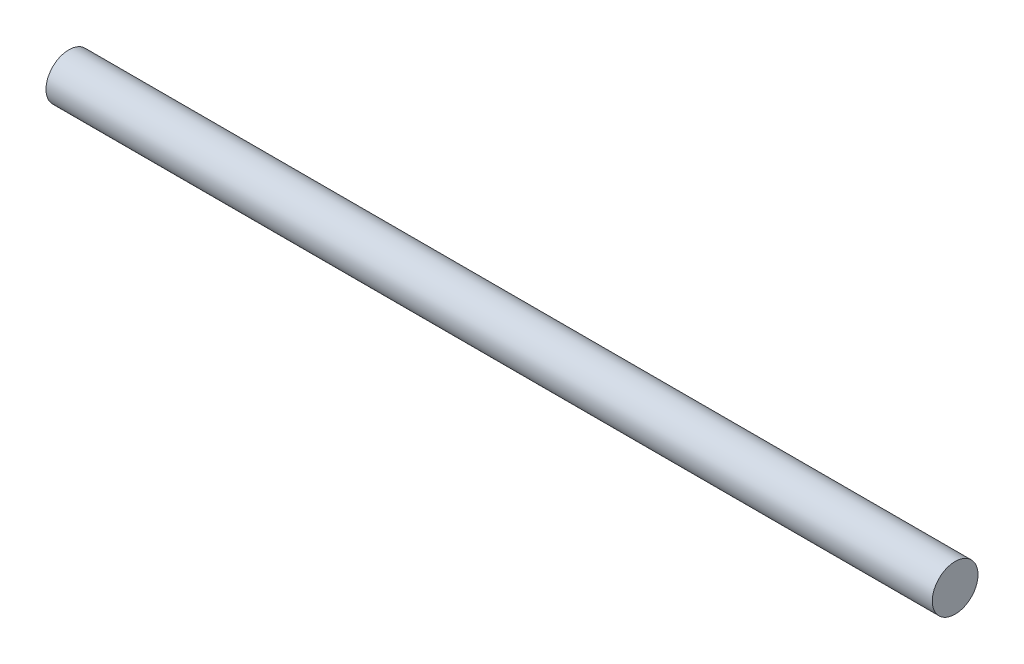
SolidWorks part; units mm, degrees
ref_plane "Front Plane" through (0, 0, 0) normal (0, 0, 1) x (1, 0, 0)
ref_plane "Top Plane" through (0, 0, 0) normal (0, 1, 0) x (1, 0, 0)
ref_plane "Right Plane" through (0, 0, 0) normal (1, 0, 0) x (0, 0, -1)
sketch "Sketch1" plane through (-4.4291, 0, 0) normal (-1, 0, 0) x (0, 0, 1)
  circle A2 centre (137.8621, 119.089) radius 2.032
  dimension "D1" = 4.064
extrude "Boss-Extrude1" add sketch "Sketch1" against normal blind 78.74
